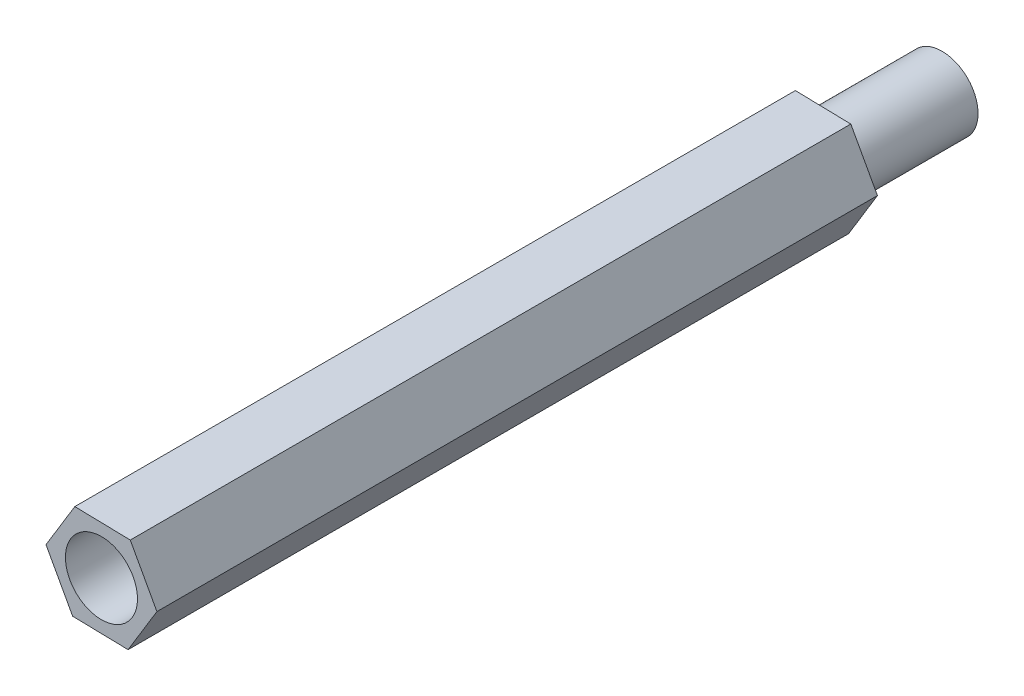
SolidWorks part; units mm, degrees
ref_plane "前视基准面" through (0, 0, 0) normal (0, 0, 1) x (1, 0, 0)
ref_plane "上视基准面" through (0, 0, 0) normal (0, 1, 0) x (1, 0, 0)
ref_plane "右视基准面" through (0, 0, 0) normal (1, 0, 0) x (0, 0, -1)
sketch "草图4" plane through (0, 0, 0) normal (0, 0, 1) x (1, 0, 0)
  line L1 (1.1088, -2.0258) -> (2.3088, -0.0526)
  line L2 (2.3088, -0.0526) -> (1.2, 1.9732)
  line L3 (1.2, 1.9732) -> (-1.1088, 2.0258)
  line L4 (-1.1088, 2.0258) -> (-2.3088, 0.0526)
  line L5 (-2.3088, 0.0526) -> (-1.2, -1.9732)
  line L6 (-1.2, -1.9732) -> (1.1088, -2.0258)
  circle A0 centre (0, 0) radius 2 construction
extrude "凸台-拉伸2" add sketch "草图4" along normal blind 30
sketch "草图5" plane through (0, 0, 0) normal (0, 0, -1) x (-1, 0, 0)
  circle A0 centre (0, 0) radius 1.4984
extrude "凸台-拉伸3" add sketch "草图5" along normal blind 5 contours A0
sketch "草图6" plane through (0, 0, 30) normal (0, 0, 1) x (1, 0, 0)
  circle A0 centre (0, 0) radius 1.5
extrude "切除-拉伸1" cut sketch "草图6" against normal blind 5 contours A0
